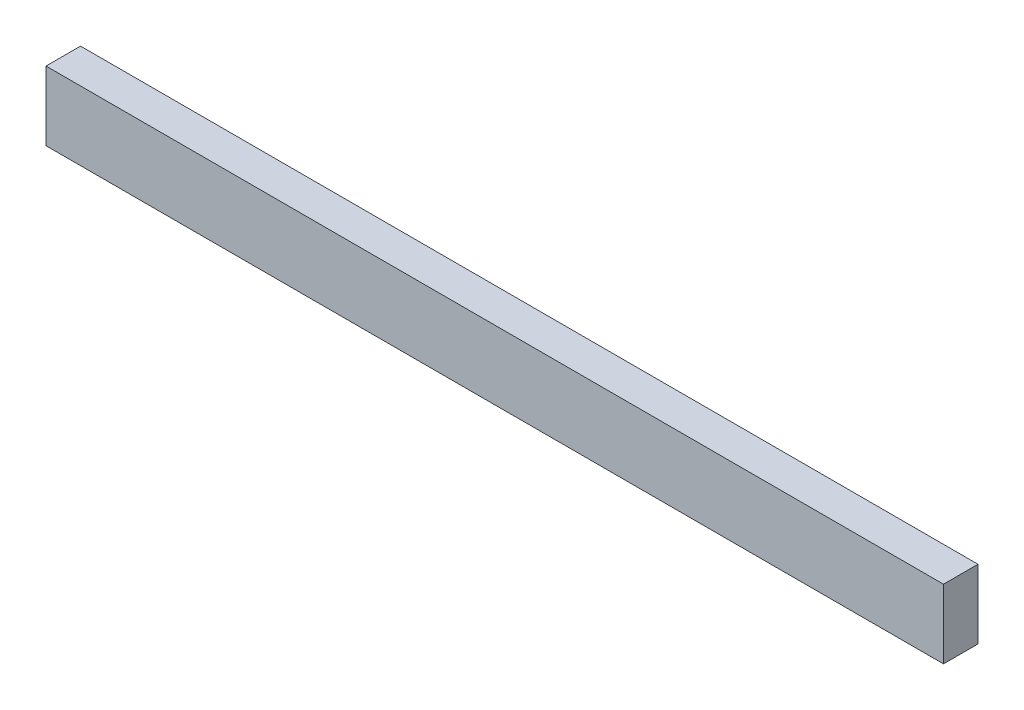
SolidWorks part; units mm, degrees
ref_plane "Front Plane" through (0, 0, 0) normal (0, 0, 1) x (1, 0, 0)
ref_plane "Top Plane" through (0, 0, 0) normal (0, 1, 0) x (1, 0, 0)
ref_plane "Right Plane" through (0, 0, 0) normal (1, 0, 0) x (0, 0, -1)
sketch "Sketch1" plane through (0, 0, 0) normal (0, 1, 0) x (1, 0, 0)
  line L1 (-139.0351, -32.9912) -> (120.9649, -32.9912)
  line L2 (-139.0351, -32.9912) -> (-139.0351, -42.9912)
  line L3 (-139.0351, -42.9912) -> (120.9649, -42.9912)
  line L4 (120.9649, -32.9912) -> (120.9649, -42.9912)
  dimension "D1" = 260
  dimension "D2" = 10
extrude "Boss-Extrude1" add sketch "Sketch1" along normal blind 20
